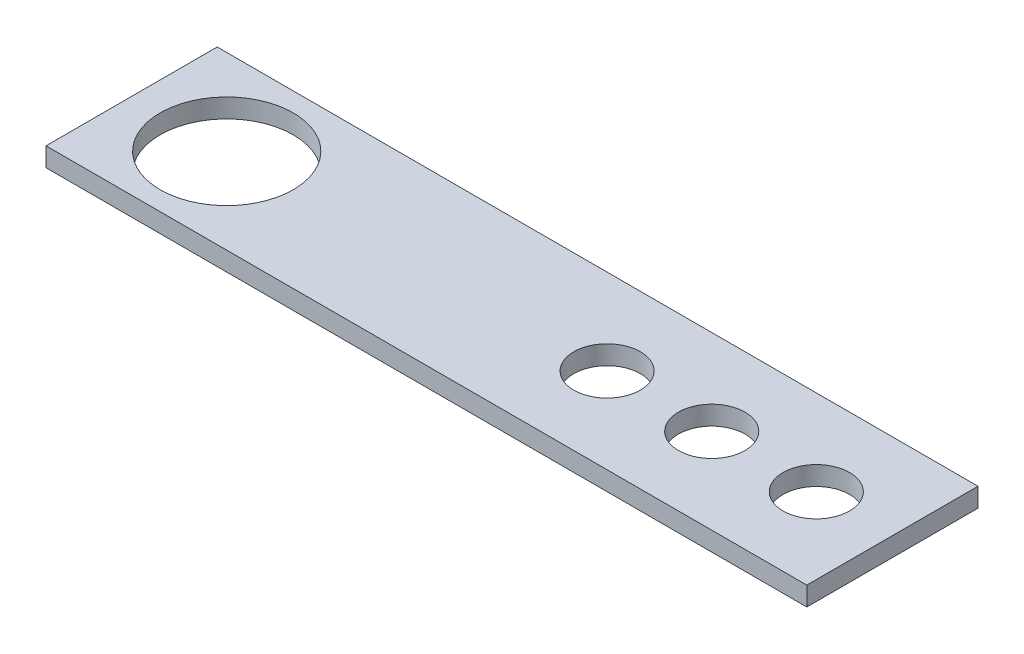
SolidWorks part; units mm, degrees
ref_plane "Front Plane" through (0, 0, 0) normal (0, 0, 1) x (1, 0, 0)
ref_plane "Top Plane" through (0, 0, 0) normal (0, 1, 0) x (1, 0, 0)
ref_plane "Right Plane" through (0, 0, 0) normal (1, 0, 0) x (0, 0, -1)
sketch "Sketch2" plane through (0, 0, 0) normal (0, 1, 0) x (1, 0, 0)
  line L1 (-20, -4.5) -> (20, -4.5)
  line L2 (-20, -4.5) -> (-20, 4.5)
  line L3 (-20, 4.5) -> (20, 4.5)
  line L4 (20, -4.5) -> (20, 4.5)
  line L5 (0, 4.5) -> (0, -4.5) construction
  line L6 (-20, 0) -> (20, 0) construction
  point P0 (0, 0)
  dimension "D1" = 9
  dimension "D2" = 40
extrude "Boss-Extrude1" add sketch "Sketch2" along normal blind 1
sketch "Sketch3" plane through (0, 1, 0) normal (0, 1, 0) x (1, 0, 0)
  line L0 (-20, 4.5) -> (-20, -4.5) construction
  line L1 (-1, 2) -> (-12.7729, 2.7)
  line L2 (-12.7729, 2.7) -> (-12.7729, -2.7)
  line L3 (-12.7729, -2.7) -> (-1, -2)
  line L4 (-20, 0) -> (20, 0) construction
  line L5 (20, -4.5) -> (20, 4.5) construction
  circle A0 centre (-15, 0) radius 3.5
  circle A1 centre (-1, 0) radius 2
  dimension "D1" = 7
  dimension "D2" = 5
  dimension "D3" = 4
  dimension "D4" = 14
  dimension "D5" = 5.4
extrude "Cut-Extrude1" cut sketch "Sketch3" against normal blind 3 contours A0
sketch "Sketch4" plane through (0, 1, 0) normal (0, 1, 0) x (1, 0, 0)
  line L0 (-20, 0) -> (20, 0) construction
  line L1 (-20, 4.5) -> (-20, -4.5) construction
  line L2 (20, -4.5) -> (20, 4.5) construction
  circle A0 centre (5, 0) radius 1.75
  circle A1 centre (-15, 0) radius 3.5 construction
  dimension "D1" = 3.5
  dimension "D2" = 20
extrude "Cut-Extrude2" cut sketch "Sketch4" against normal blind 3
pattern_linear "LPattern1" count 3 spacing 5.5 along (1, 0, 0) of "Cut-Extrude2"
